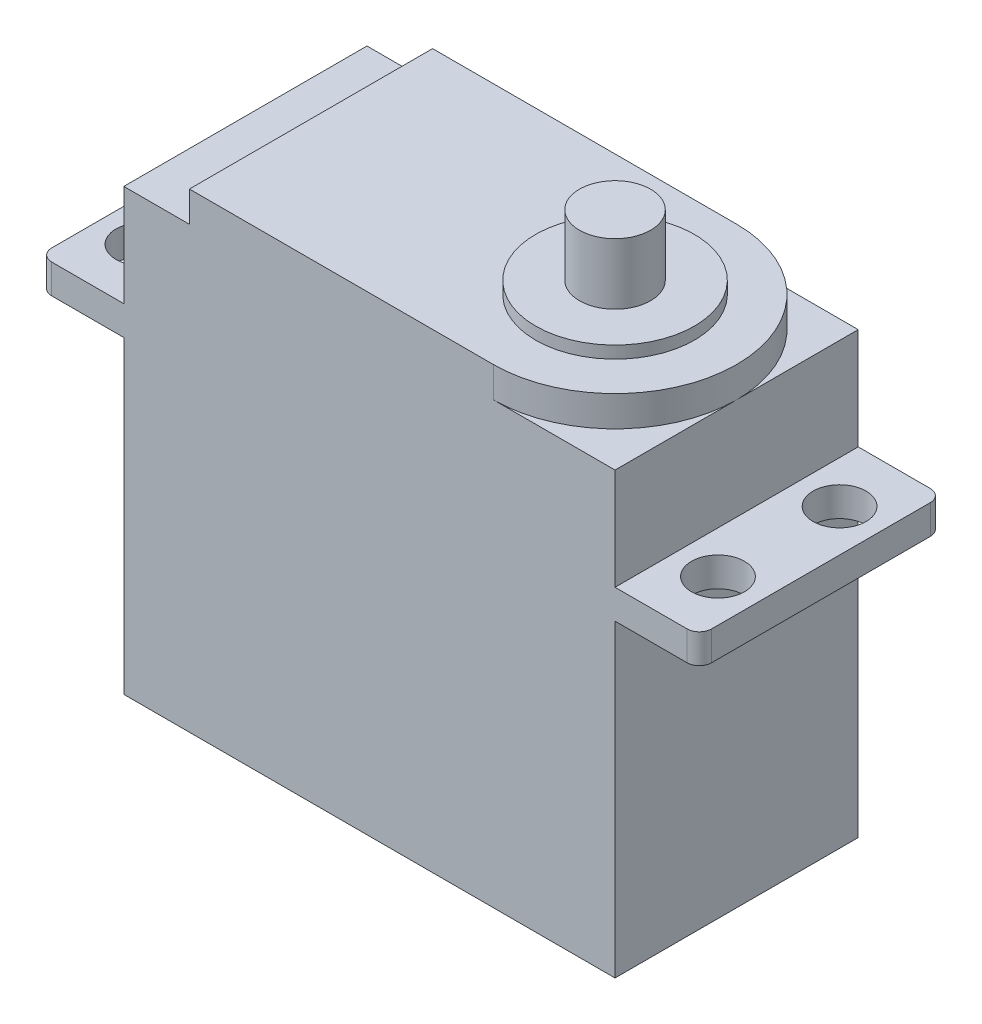
SolidWorks part; units mm, degrees
ref_plane "Alzado" through (0, 0, 0) normal (0, 0, 1) x (1, 0, 0)
ref_plane "Planta" through (0, 0, 0) normal (0, 1, 0) x (1, 0, 0)
ref_plane "Vista lateral" through (0, 0, 0) normal (1, 0, 0) x (0, 0, -1)
sketch "Croquis1" plane through (0, 0, 0) normal (0, 1, 0) x (1, 0, 0)
  line L1 (-20.1, 9.95) -> (20.1, 9.95)
  line L2 (-20.1, 9.95) -> (-20.1, -9.95)
  line L3 (-20.1, -9.95) -> (20.1, -9.95)
  line L4 (20.1, 9.95) -> (20.1, -9.95)
  line L5 (-20.1, 9.95) -> (20.1, -9.95) construction
  line L6 (-20.1, -9.95) -> (20.1, 9.95) construction
  point P0 (0, 0)
  dimension "D1" = 19.9
  dimension "D2" = 40.2
extrude "Saliente-Extruir1" add sketch "Croquis1" along normal blind 36
sketch "Croquis4" plane through (0, 0, 0) normal (1, 0, 0) x (0, 0, -1)
  line L0 (0, 36) -> (0, 27.69) construction
  line L1 (-9.95, 36) -> (9.95, 36) construction
  line L2 (-9.95, 27.69) -> (9.95, 27.69)
  line L3 (9.95, 36) -> (9.95, 0) construction
  line L4 (9.95, 27.69) -> (9.95, 25.29)
  line L5 (9.95, 25.29) -> (-9.95, 25.29)
  line L6 (-9.95, 36) -> (-9.95, 0) construction
  line L7 (-9.95, 25.29) -> (-9.95, 27.69)
  point P10 (0, 27.69)
  dimension "D1" = 8.31
  dimension "D2" = 2.4
extrude "Saliente-Extruir3" add sketch "Croquis4" along normal mid plane 54
sketch "Croquis5" plane through (0, 27.69, 0) normal (0, 1, 0) x (1, 0, 0)
  line L0 (-20.1, 0) -> (-27, 0) construction
  line L3 (-20.1, 9.95) -> (-20.1, -9.95) construction
  line L4 (-27, 9.95) -> (-27, -9.95) construction
  line L5 (20.1, 0) -> (27, 0) construction
  line L8 (-23.55, 0) -> (-23.55, 9.95) construction
  line L9 (20.1, 9.95) -> (20.1, -9.95) construction
  line L11 (27, 9.95) -> (27, -9.95) construction
  line L12 (23.55, 9.95) -> (23.55, 0) construction
  line L13 (27, 9.95) -> (20.1, 9.95) construction
  line L14 (-20.1, 9.95) -> (-27, 9.95) construction
  line L15 (-23.55, 0) -> (-23.55, -9.95) construction
  line L16 (-20.1, -9.95) -> (-27, -9.95) construction
  line L17 (23.55, 0) -> (23.55, -9.95) construction
  line L18 (27, -9.95) -> (20.1, -9.95) construction
  circle A4 centre (-23.55, 4.975) radius 2.165
  circle A5 centre (-23.55, -4.975) radius 2.165
  circle A6 centre (23.55, 4.975) radius 2.165
  circle A7 centre (23.55, -4.975) radius 2.165
  point P15 (-23.55, 0)
  point P18 (23.55, 0)
  dimension "D1" = 4.33
  dimension "D2" = 4.33
  dimension "D3" = 4.33
  dimension "D4" = 4.33
extrude "Cortar-Extruir2" cut sketch "Croquis5" against normal blind 57.31
sketch "Croquis6" plane through (0, 36, 0) normal (0, 1, 0) x (1, 0, 0)
  line L0 (-20.1, -9.95) -> (-20.1, 9.95) construction
  line L3 (20.1, -9.95) -> (20.1, 9.95) construction
  line L4 (10.15, 9.95) -> (-14.73, 9.95)
  line L5 (20.1, 9.95) -> (-20.1, 9.95) construction
  line L6 (-14.73, 9.95) -> (-14.73, -9.95)
  line L7 (-20.1, -9.95) -> (20.1, -9.95) construction
  line L8 (-14.73, -9.95) -> (10.15, -9.95)
  line L9 (10.15, -9.95) -> (10.15, 9.95)
  circle A0 centre (10.15, 0) radius 9.95
  line M3 (20.1, 9.95) -> (-20.1, 9.95)
  line M5 (-20.1, -9.95) -> (20.1, -9.95)
  dimension "D1" = 19.9
  dimension "D2" = 9.95
  dimension "D3" = 5.37
extrude "Saliente-Extruir5" add sketch "Croquis6" along normal blind 2.5 contours A0 L6 M3 M5 | L9 A0 | L9 A0
sketch "Croquis7" plane through (0, 38.5, 0) normal (0, 1, 0) x (1, 0, 0)
  line L0 (10.15, -29.85) -> (10.15, 9.95)
  arc A0 (10.15, -9.95) -> (10.15, 9.95) centre (10.15, 0) ccw construction
  circle A1 centre (10.15, 0) radius 6.5
  point P7 (10.15, -9.95)
  dimension "D1" = 13
extrude "Saliente-Extruir6" add sketch "Croquis7" along normal blind 1 contours L0 A1 | L0 A1
sketch "Croquis8" plane through (0, 39.5, 0) normal (0, 1, 0) x (1, 0, 0)
  circle A0 centre (10.15, 0) radius 2.91
  dimension "D1" = 5.82
extrude "Saliente-Extruir7" add sketch "Croquis8" along normal blind 5
fillet "Redondeo1" radius 1 4 edges at (27, 26.49, 9.95) (27, 26.49, -9.95) (-27, 26.49, -9.95) (-27, 26.49, 9.95)
